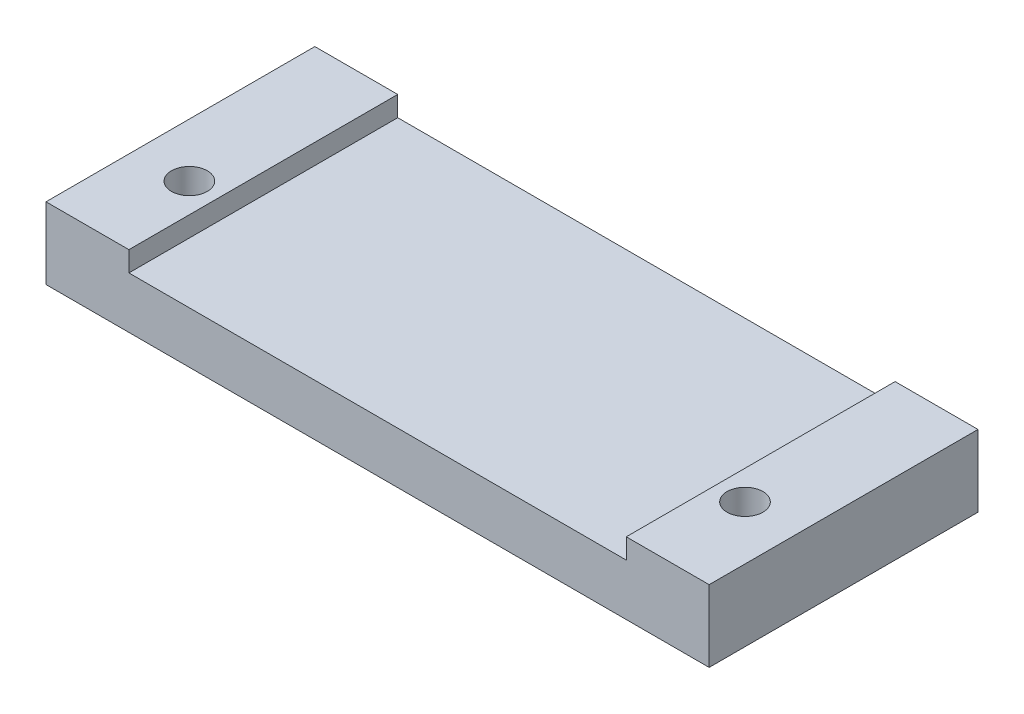
SolidWorks part; units mm, degrees
ref_plane "Front Plane" through (0, 0, 0) normal (0, 0, 1) x (1, 0, 0)
ref_plane "Top Plane" through (0, 0, 0) normal (0, 1, 0) x (1, 0, 0)
ref_plane "Right Plane" through (0, 0, 0) normal (1, 0, 0) x (0, 0, -1)
sketch "Sketch1" plane through (0, 0, 0) normal (0, 1, 0) x (1, 0, 0)
  line L1 (0, 0) -> (74, 0)
  line L2 (0, 0) -> (0, 30)
  line L3 (0, 30) -> (74, 30)
  line L4 (74, 0) -> (74, 30)
  dimension "D1" = 74
  dimension "D2" = 30
extrude "Boss-Extrude1" add sketch "Sketch1" along normal blind 5.75
sketch "Sketch2" plane through (0, 5.75, 0) normal (0, 1, 0) x (1, 0, 0)
  line L0 (0, 30) -> (0, 0) construction
  line L1 (0, 30) -> (9.25, 30)
  line L2 (0, 30) -> (0, 0)
  line L3 (0, 0) -> (9.25, 0)
  line L4 (9.25, 30) -> (9.25, 0)
  line L5 (0, 0) -> (74, 0) construction
  line L7 (74, 30) -> (64.75, 30)
  line L8 (74, 30) -> (74, 0)
  line L9 (74, 0) -> (64.75, 0)
  line L10 (64.75, 30) -> (64.75, 0)
  dimension "D1" = 9.25
extrude "Boss-Extrude2" add sketch "Sketch2" along normal blind 2.25
sketch "Sketch3" plane through (0, 0, 0) normal (0, -1, 0) x (-1, 0, 0)
  line L0 (0, 0) -> (-74, 0) construction
  line L1 (-74, 0) -> (-74, 30) construction
  line L2 (0, 30) -> (0, 0) construction
  circle A0 centre (-68, 10) radius 2
  circle A1 centre (-6, 10) radius 2
  point P8 (0, 0)
  dimension "D1" = 4
  dimension "D2" = 10
  dimension "D3" = 6
  dimension "D4" = 6
extrude "Cut-Extrude1" cut sketch "Sketch3" against normal through all
